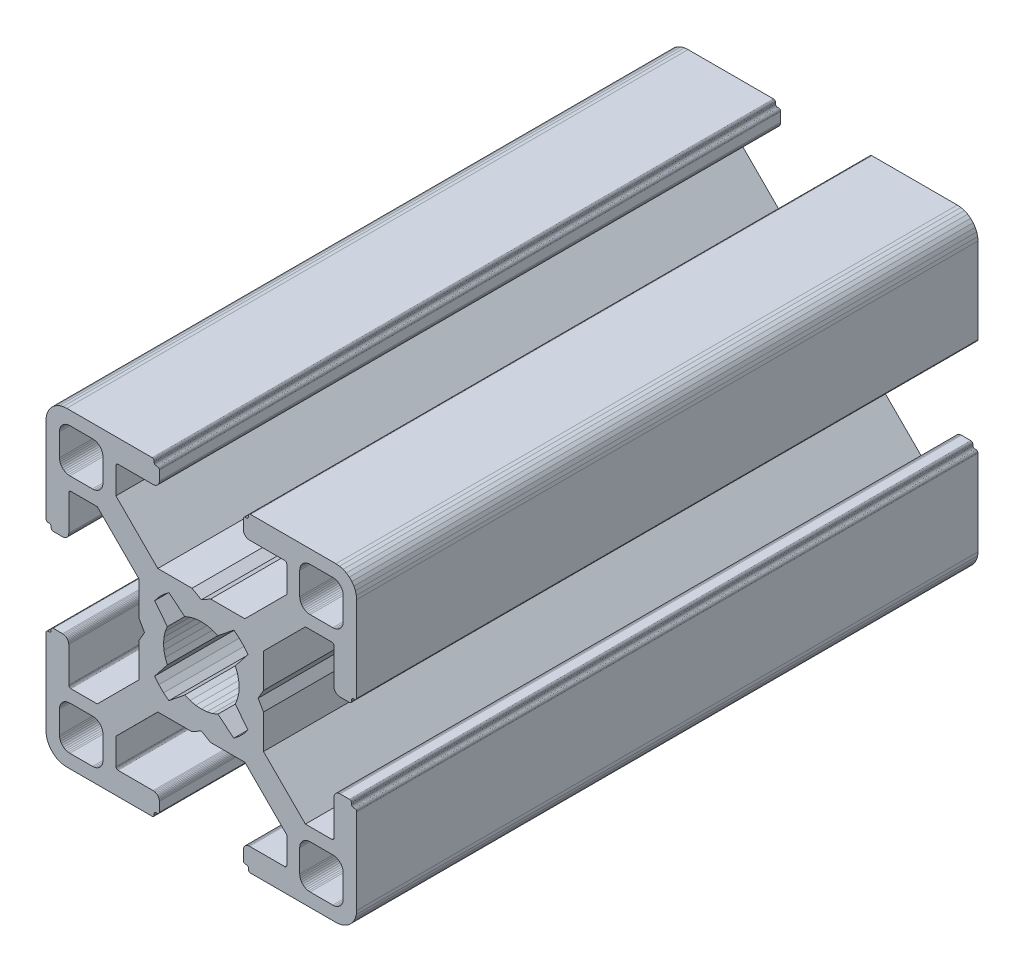
SolidWorks part; units mm, degrees
ref_plane "Front Plane" through (0, 0, 0) normal (0, 0, 1) x (1, 0, 0)
ref_plane "Top Plane" through (0, 0, 0) normal (0, 1, 0) x (1, 0, 0)
ref_plane "Right Plane" through (0, 0, 0) normal (1, 0, 0) x (0, 0, -1)
ref_plane "Plane1" through (0, 0, 0) normal (0, 0, 1) x (1, 0, 0)
sketch "Sketch1" plane through (0, 0, 0) normal (0, 0, 1) x (1, 0, 0)
  line L0 (28.3473, 29.9696) -> (28, 30)
  line L1 (28, 30) -> (19.75, 30)
  line L2 (19.75, 30) -> (19.7153, 29.997)
  line L3 (19.7153, 29.997) -> (19.6816, 29.9879)
  line L4 (19.6816, 29.9879) -> (19.65, 29.9732)
  line L5 (19.65, 29.9732) -> (19.6214, 29.9532)
  line L6 (19.6214, 29.9532) -> (19.5968, 29.9286)
  line L7 (19.5968, 29.9286) -> (19.5768, 29.9)
  line L8 (19.5768, 29.9) -> (19.5621, 29.8684)
  line L9 (19.5621, 29.8684) -> (19.553, 29.8347)
  line L10 (19.553, 29.8347) -> (19.55, 29.8)
  line L11 (19.55, 29.8) -> (19.55, 29.7)
  line L12 (19.55, 29.7) -> (19.547, 29.6653)
  line L13 (19.547, 29.6653) -> (19.5379, 29.6316)
  line L14 (19.5379, 29.6316) -> (19.5232, 29.6)
  line L15 (19.5232, 29.6) -> (19.5032, 29.5714)
  line L16 (19.5032, 29.5714) -> (19.4786, 29.5468)
  line L17 (19.4786, 29.5468) -> (19.45, 29.5268)
  line L18 (19.45, 29.5268) -> (19.4184, 29.5121)
  line L19 (19.4184, 29.5121) -> (19.3847, 29.503)
  line L20 (19.3847, 29.503) -> (19.35, 29.5)
  line L21 (19.35, 29.5) -> (19.25, 29.5)
  line L22 (19.25, 29.5) -> (19.2153, 29.497)
  line L23 (19.2153, 29.497) -> (19.1816, 29.4879)
  line L24 (19.1816, 29.4879) -> (19.15, 29.4732)
  line L25 (19.15, 29.4732) -> (19.1214, 29.4532)
  line L26 (19.1214, 29.4532) -> (19.0968, 29.4286)
  line L27 (19.0968, 29.4286) -> (19.0768, 29.4)
  line L28 (19.0768, 29.4) -> (19.0621, 29.3684)
  line L29 (19.0621, 29.3684) -> (19.053, 29.3347)
  line L30 (19.053, 29.3347) -> (19.05, 29.3)
  line L31 (19.05, 29.3) -> (19.05, 28.4)
  line L32 (19.05, 28.4) -> (19.0591, 28.2958)
  line L33 (19.0591, 28.2958) -> (19.0862, 28.1948)
  line L34 (19.0862, 28.1948) -> (19.1304, 28.1)
  line L35 (19.1304, 28.1) -> (19.1904, 28.0143)
  line L36 (19.1904, 28.0143) -> (19.2643, 27.9404)
  line L37 (19.2643, 27.9404) -> (19.35, 27.8804)
  line L38 (19.35, 27.8804) -> (19.4448, 27.8362)
  line L39 (19.4448, 27.8362) -> (19.5458, 27.8091)
  line L40 (19.5458, 27.8091) -> (19.65, 27.8)
  line L41 (19.65, 27.8) -> (23.05, 27.8)
  line L42 (23.05, 27.8) -> (23.0847, 27.7969)
  line L43 (23.0847, 27.7969) -> (23.1184, 27.7879)
  line L44 (23.1184, 27.7879) -> (23.15, 27.7732)
  line L45 (23.15, 27.7732) -> (23.1786, 27.7532)
  line L46 (23.1786, 27.7532) -> (23.2032, 27.7285)
  line L47 (23.2032, 27.7285) -> (23.2232, 27.7)
  line L48 (23.2232, 27.7) -> (23.2379, 27.6684)
  line L49 (23.2379, 27.6684) -> (23.247, 27.6347)
  line L50 (23.247, 27.6347) -> (23.25, 27.6)
  line L51 (23.25, 27.6) -> (23.25, 25.05)
  line L52 (23.25, 25.05) -> (19.2045, 21)
  line L53 (19.2045, 21) -> (15.9, 21)
  line L54 (15.9, 21) -> (15, 20.4848)
  line L55 (15, 20.4848) -> (14.1, 21)
  line L56 (14.1, 21) -> (10.7955, 21)
  line L57 (10.7955, 21) -> (7.9973, 23.8013)
  line L58 (7.9973, 23.8013) -> (6.75, 25.05)
  line L59 (6.75, 25.05) -> (6.75, 27.6)
  line L60 (6.75, 27.6) -> (6.753, 27.6347)
  line L61 (6.753, 27.6347) -> (6.7621, 27.6684)
  line L62 (6.7621, 27.6684) -> (6.7768, 27.7)
  line L63 (6.7768, 27.7) -> (6.7968, 27.7285)
  line L64 (6.7968, 27.7285) -> (6.8215, 27.7532)
  line L65 (6.8215, 27.7532) -> (6.85, 27.7732)
  line L66 (6.85, 27.7732) -> (6.8816, 27.7879)
  line L67 (6.8816, 27.7879) -> (6.9153, 27.7969)
  line L68 (6.9153, 27.7969) -> (6.95, 27.8)
  line L69 (6.95, 27.8) -> (10.35, 27.8)
  line L70 (10.35, 27.8) -> (10.4542, 27.8091)
  line L71 (10.4542, 27.8091) -> (10.5552, 27.8362)
  line L72 (10.5552, 27.8362) -> (10.65, 27.8804)
  line L73 (10.65, 27.8804) -> (10.7357, 27.9404)
  line L74 (10.7357, 27.9404) -> (10.8096, 28.0143)
  line L75 (10.8096, 28.0143) -> (10.8696, 28.1)
  line L76 (10.8696, 28.1) -> (10.9138, 28.1948)
  line L77 (10.9138, 28.1948) -> (10.9409, 28.2958)
  line L78 (10.9409, 28.2958) -> (10.95, 28.4)
  line L79 (10.95, 28.4) -> (10.95, 29.3)
  line L80 (10.95, 29.3) -> (10.947, 29.3347)
  line L81 (10.947, 29.3347) -> (10.938, 29.3684)
  line L82 (10.938, 29.3684) -> (10.9232, 29.4)
  line L83 (10.9232, 29.4) -> (10.9032, 29.4286)
  line L84 (10.9032, 29.4286) -> (10.8786, 29.4532)
  line L85 (10.8786, 29.4532) -> (10.85, 29.4732)
  line L86 (10.85, 29.4732) -> (10.8184, 29.4879)
  line L87 (10.8184, 29.4879) -> (10.7847, 29.497)
  line L88 (10.7847, 29.497) -> (10.75, 29.5)
  line L89 (10.75, 29.5) -> (10.65, 29.5)
  line L90 (10.65, 29.5) -> (10.6153, 29.503)
  line L91 (10.6153, 29.503) -> (10.5816, 29.5121)
  line L92 (10.5816, 29.5121) -> (10.55, 29.5268)
  line L93 (10.55, 29.5268) -> (10.5214, 29.5468)
  line L94 (10.5214, 29.5468) -> (10.4968, 29.5714)
  line L95 (10.4968, 29.5714) -> (10.4768, 29.6)
  line L96 (10.4768, 29.6) -> (10.4621, 29.6316)
  line L97 (10.4621, 29.6316) -> (10.453, 29.6653)
  line L98 (10.453, 29.6653) -> (10.45, 29.7)
  line L99 (10.45, 29.7) -> (10.45, 29.8)
  line L100 (10.45, 29.8) -> (10.447, 29.8347)
  line L101 (10.447, 29.8347) -> (10.4379, 29.8684)
  line L102 (10.4379, 29.8684) -> (10.4232, 29.9)
  line L103 (10.4232, 29.9) -> (10.4032, 29.9286)
  line L104 (10.4032, 29.9286) -> (10.3786, 29.9532)
  line L105 (10.3786, 29.9532) -> (10.35, 29.9732)
  line L106 (10.35, 29.9732) -> (10.3184, 29.9879)
  line L107 (10.3184, 29.9879) -> (10.2847, 29.997)
  line L108 (10.2847, 29.997) -> (10.25, 30)
  line L109 (10.25, 30) -> (2, 30)
  line L110 (2, 30) -> (1.6527, 29.9696)
  line L111 (1.6527, 29.9696) -> (1.316, 29.8794)
  line L112 (1.316, 29.8794) -> (1, 29.7321)
  line L113 (1, 29.7321) -> (0.7144, 29.5321)
  line L114 (0.7144, 29.5321) -> (0.4679, 29.2856)
  line L115 (0.4679, 29.2856) -> (0.2679, 29)
  line L116 (0.2679, 29) -> (0.1206, 28.684)
  line L117 (0.1206, 28.684) -> (0.0304, 28.3473)
  line L118 (0.0304, 28.3473) -> (0, 28)
  line L119 (0, 28) -> (0, 19.75)
  line L120 (0, 19.75) -> (0.003, 19.7153)
  line L121 (0.003, 19.7153) -> (0.0121, 19.6816)
  line L122 (0.0121, 19.6816) -> (0.0268, 19.65)
  line L123 (0.0268, 19.65) -> (0.0468, 19.6214)
  line L124 (0.0468, 19.6214) -> (0.0714, 19.5968)
  line L125 (0.0714, 19.5968) -> (0.1, 19.5768)
  line L126 (0.1, 19.5768) -> (0.1316, 19.5621)
  line L127 (0.1316, 19.5621) -> (0.1653, 19.553)
  line L128 (0.1653, 19.553) -> (0.2, 19.55)
  line L129 (0.2, 19.55) -> (0.3, 19.55)
  line L130 (0.3, 19.55) -> (0.3347, 19.547)
  line L131 (0.3347, 19.547) -> (0.3684, 19.5379)
  line L132 (0.3684, 19.5379) -> (0.4, 19.5232)
  line L133 (0.4, 19.5232) -> (0.4286, 19.5032)
  line L134 (0.4286, 19.5032) -> (0.4532, 19.4786)
  line L135 (0.4532, 19.4786) -> (0.4732, 19.45)
  line L136 (0.4732, 19.45) -> (0.4879, 19.4184)
  line L137 (0.4879, 19.4184) -> (0.497, 19.3847)
  line L138 (0.497, 19.3847) -> (0.5, 19.35)
  line L139 (0.5, 19.35) -> (0.5, 19.25)
  line L140 (0.5, 19.25) -> (0.503, 19.2153)
  line L141 (0.503, 19.2153) -> (0.5121, 19.1816)
  line L142 (0.5121, 19.1816) -> (0.5268, 19.15)
  line L143 (0.5268, 19.15) -> (0.5468, 19.1214)
  line L144 (0.5468, 19.1214) -> (0.5714, 19.0968)
  line L145 (0.5714, 19.0968) -> (0.6, 19.0768)
  line L146 (0.6, 19.0768) -> (0.6316, 19.0621)
  line L147 (0.6316, 19.0621) -> (0.6653, 19.053)
  line L148 (0.6653, 19.053) -> (0.7, 19.05)
  line L149 (0.7, 19.05) -> (1.6, 19.05)
  line L150 (1.6, 19.05) -> (1.7042, 19.0591)
  line L151 (1.7042, 19.0591) -> (1.8052, 19.0862)
  line L152 (1.8052, 19.0862) -> (1.9, 19.1304)
  line L153 (1.9, 19.1304) -> (1.9857, 19.1904)
  line L154 (1.9857, 19.1904) -> (2.0596, 19.2643)
  line L155 (2.0596, 19.2643) -> (2.1196, 19.35)
  line L156 (2.1196, 19.35) -> (2.1638, 19.4448)
  line L157 (2.1638, 19.4448) -> (2.1909, 19.5458)
  line L158 (2.1909, 19.5458) -> (2.2, 19.65)
  line L159 (2.2, 19.65) -> (2.2, 23.05)
  line L160 (2.2, 23.05) -> (2.203, 23.0847)
  line L161 (2.203, 23.0847) -> (2.2121, 23.1184)
  line L162 (2.2121, 23.1184) -> (2.2268, 23.15)
  line L163 (2.2268, 23.15) -> (2.2468, 23.1786)
  line L164 (2.2468, 23.1786) -> (2.2714, 23.2032)
  line L165 (2.2714, 23.2032) -> (2.3, 23.2232)
  line L166 (2.3, 23.2232) -> (2.3316, 23.2379)
  line L167 (2.3316, 23.2379) -> (2.3653, 23.247)
  line L168 (2.3653, 23.247) -> (2.4, 23.25)
  line L169 (2.4, 23.25) -> (4.95, 23.25)
  line L170 (4.95, 23.25) -> (7.9973, 20.2027)
  line L171 (7.9973, 20.2027) -> (8.9955, 19.2045)
  line L172 (8.9955, 19.2045) -> (8.9955, 15.9)
  line L173 (8.9955, 15.9) -> (9.5151, 15)
  line L174 (9.5151, 15) -> (8.9955, 14.1)
  line L175 (8.9955, 14.1) -> (8.9955, 10.7955)
  line L176 (8.9955, 10.7955) -> (4.95, 6.75)
  line L177 (4.95, 6.75) -> (2.4, 6.75)
  line L178 (2.4, 6.75) -> (2.3653, 6.753)
  line L179 (2.3653, 6.753) -> (2.3316, 6.7621)
  line L180 (2.3316, 6.7621) -> (2.3, 6.7768)
  line L181 (2.3, 6.7768) -> (2.2714, 6.7968)
  line L182 (2.2714, 6.7968) -> (2.2468, 6.8214)
  line L183 (2.2468, 6.8214) -> (2.2268, 6.85)
  line L184 (2.2268, 6.85) -> (2.2121, 6.8816)
  line L185 (2.2121, 6.8816) -> (2.203, 6.9153)
  line L186 (2.203, 6.9153) -> (2.2, 6.95)
  line L187 (2.2, 6.95) -> (2.2, 10.35)
  line L188 (2.2, 10.35) -> (2.1909, 10.4542)
  line L189 (2.1909, 10.4542) -> (2.1638, 10.5552)
  line L190 (2.1638, 10.5552) -> (2.1196, 10.65)
  line L191 (2.1196, 10.65) -> (2.0596, 10.7357)
  line L192 (2.0596, 10.7357) -> (1.9857, 10.8096)
  line L193 (1.9857, 10.8096) -> (1.9, 10.8696)
  line L194 (1.9, 10.8696) -> (1.8052, 10.9138)
  line L195 (1.8052, 10.9138) -> (1.7042, 10.9409)
  line L196 (1.7042, 10.9409) -> (1.6, 10.95)
  line L197 (1.6, 10.95) -> (0.7, 10.95)
  line L198 (0.7, 10.95) -> (0.6653, 10.9469)
  line L199 (0.6653, 10.9469) -> (0.6316, 10.9379)
  line L200 (0.6316, 10.9379) -> (0.6, 10.9232)
  line L201 (0.6, 10.9232) -> (0.5715, 10.9032)
  line L202 (0.5715, 10.9032) -> (0.5468, 10.8785)
  line L203 (0.5468, 10.8785) -> (0.5268, 10.85)
  line L204 (0.5268, 10.85) -> (0.5121, 10.8184)
  line L205 (0.5121, 10.8184) -> (0.503, 10.7847)
  line L206 (0.503, 10.7847) -> (0.5, 10.75)
  line L207 (0.5, 10.75) -> (0.5, 10.65)
  line L208 (0.5, 10.65) -> (0.497, 10.6153)
  line L209 (0.497, 10.6153) -> (0.4879, 10.5816)
  line L210 (0.4879, 10.5816) -> (0.4732, 10.55)
  line L211 (0.4732, 10.55) -> (0.4532, 10.5214)
  line L212 (0.4532, 10.5214) -> (0.4286, 10.4968)
  line L213 (0.4286, 10.4968) -> (0.4, 10.4768)
  line L214 (0.4, 10.4768) -> (0.3684, 10.4621)
  line L215 (0.3684, 10.4621) -> (0.3347, 10.453)
  line L216 (0.3347, 10.453) -> (0.3, 10.45)
  line L217 (0.3, 10.45) -> (0.2, 10.45)
  line L218 (0.2, 10.45) -> (0.1653, 10.447)
  line L219 (0.1653, 10.447) -> (0.1316, 10.4379)
  line L220 (0.1316, 10.4379) -> (0.1, 10.4232)
  line L221 (0.1, 10.4232) -> (0.0714, 10.4032)
  line L222 (0.0714, 10.4032) -> (0.0468, 10.3786)
  line L223 (0.0468, 10.3786) -> (0.0268, 10.35)
  line L224 (0.0268, 10.35) -> (0.0121, 10.3184)
  line L225 (0.0121, 10.3184) -> (0.003, 10.2847)
  line L226 (0.003, 10.2847) -> (0, 10.25)
  line L227 (0, 10.25) -> (0, 2)
  line L228 (0, 2) -> (0.0304, 1.6527)
  line L229 (0.0304, 1.6527) -> (0.1206, 1.316)
  line L230 (0.1206, 1.316) -> (0.2679, 1)
  line L231 (0.2679, 1) -> (0.4679, 0.7144)
  line L232 (0.4679, 0.7144) -> (0.7144, 0.4679)
  line L233 (0.7144, 0.4679) -> (1, 0.2679)
  line L234 (1, 0.2679) -> (1.316, 0.1206)
  line L235 (1.316, 0.1206) -> (1.6527, 0.0304)
  line L236 (1.6527, 0.0304) -> (2, 0)
  line L237 (2, 0) -> (10.25, 0)
  line L238 (10.25, 0) -> (10.2847, 0.003)
  line L239 (10.2847, 0.003) -> (10.3184, 0.0121)
  line L240 (10.3184, 0.0121) -> (10.35, 0.0268)
  line L241 (10.35, 0.0268) -> (10.3786, 0.0468)
  line L242 (10.3786, 0.0468) -> (10.4032, 0.0714)
  line L243 (10.4032, 0.0714) -> (10.4232, 0.1)
  line L244 (10.4232, 0.1) -> (10.4379, 0.1316)
  line L245 (10.4379, 0.1316) -> (10.447, 0.1653)
  line L246 (10.447, 0.1653) -> (10.45, 0.2)
  line L247 (10.45, 0.2) -> (10.45, 0.3)
  line L248 (10.45, 0.3) -> (10.453, 0.3347)
  line L249 (10.453, 0.3347) -> (10.4621, 0.3684)
  line L250 (10.4621, 0.3684) -> (10.4768, 0.4)
  line L251 (10.4768, 0.4) -> (10.4968, 0.4286)
  line L252 (10.4968, 0.4286) -> (10.5214, 0.4532)
  line L253 (10.5214, 0.4532) -> (10.55, 0.4732)
  line L254 (10.55, 0.4732) -> (10.5816, 0.4879)
  line L255 (10.5816, 0.4879) -> (10.6153, 0.497)
  line L256 (10.6153, 0.497) -> (10.65, 0.5)
  line L257 (10.65, 0.5) -> (10.75, 0.5)
  line L258 (10.75, 0.5) -> (10.7847, 0.503)
  line L259 (10.7847, 0.503) -> (10.8184, 0.5121)
  line L260 (10.8184, 0.5121) -> (10.85, 0.5268)
  line L261 (10.85, 0.5268) -> (10.8785, 0.5468)
  line L262 (10.8785, 0.5468) -> (10.9032, 0.5715)
  line L263 (10.9032, 0.5715) -> (10.9232, 0.6)
  line L264 (10.9232, 0.6) -> (10.9379, 0.6316)
  line L265 (10.9379, 0.6316) -> (10.9469, 0.6653)
  line L266 (10.9469, 0.6653) -> (10.95, 0.7)
  line L267 (10.95, 0.7) -> (10.95, 1.6)
  line L268 (10.95, 1.6) -> (10.9409, 1.7042)
  line L269 (10.9409, 1.7042) -> (10.9138, 1.8052)
  line L270 (10.9138, 1.8052) -> (10.8696, 1.9)
  line L271 (10.8696, 1.9) -> (10.8096, 1.9857)
  line L272 (10.8096, 1.9857) -> (10.7357, 2.0596)
  line L273 (10.7357, 2.0596) -> (10.65, 2.1196)
  line L274 (10.65, 2.1196) -> (10.5552, 2.1638)
  line L275 (10.5552, 2.1638) -> (10.4542, 2.1909)
  line L276 (10.4542, 2.1909) -> (10.35, 2.2)
  line L277 (10.35, 2.2) -> (6.95, 2.2)
  line L278 (6.95, 2.2) -> (6.9153, 2.203)
  line L279 (6.9153, 2.203) -> (6.8816, 2.212)
  line L280 (6.8816, 2.212) -> (6.85, 2.2268)
  line L281 (6.85, 2.2268) -> (6.8215, 2.2468)
  line L282 (6.8215, 2.2468) -> (6.7968, 2.2714)
  line L283 (6.7968, 2.2714) -> (6.7768, 2.3)
  line L284 (6.7768, 2.3) -> (6.7621, 2.3316)
  line L285 (6.7621, 2.3316) -> (6.753, 2.3653)
  line L286 (6.753, 2.3653) -> (6.75, 2.4)
  line L287 (6.75, 2.4) -> (6.75, 4.95)
  line L288 (6.75, 4.95) -> (9.7875, 7.9908)
  line L289 (9.7875, 7.9908) -> (10.7955, 9)
  line L290 (10.7955, 9) -> (14.1, 9)
  line L291 (14.1, 9) -> (15, 9.5151)
  line L292 (15, 9.5151) -> (15.9, 9)
  line L293 (15.9, 9) -> (19.2045, 9)
  line L294 (19.2045, 9) -> (20.2126, 7.9908)
  line L295 (20.2126, 7.9908) -> (23.25, 4.95)
  line L296 (23.25, 4.95) -> (23.25, 2.4)
  line L297 (23.25, 2.4) -> (23.247, 2.3653)
  line L298 (23.247, 2.3653) -> (23.2379, 2.3316)
  line L299 (23.2379, 2.3316) -> (23.2232, 2.3)
  line L300 (23.2232, 2.3) -> (23.2032, 2.2714)
  line L301 (23.2032, 2.2714) -> (23.1786, 2.2468)
  line L302 (23.1786, 2.2468) -> (23.15, 2.2268)
  line L303 (23.15, 2.2268) -> (23.1184, 2.212)
  line L304 (23.1184, 2.212) -> (23.0847, 2.203)
  line L305 (23.0847, 2.203) -> (23.05, 2.2)
  line L306 (23.05, 2.2) -> (19.65, 2.2)
  line L307 (19.65, 2.2) -> (19.5458, 2.1909)
  line L308 (19.5458, 2.1909) -> (19.4448, 2.1638)
  line L309 (19.4448, 2.1638) -> (19.35, 2.1196)
  line L310 (19.35, 2.1196) -> (19.2643, 2.0596)
  line L311 (19.2643, 2.0596) -> (19.1904, 1.9857)
  line L312 (19.1904, 1.9857) -> (19.1304, 1.9)
  line L313 (19.1304, 1.9) -> (19.0862, 1.8052)
  line L314 (19.0862, 1.8052) -> (19.0591, 1.7042)
  line L315 (19.0591, 1.7042) -> (19.05, 1.6)
  line L316 (19.05, 1.6) -> (19.05, 0.7)
  line L317 (19.05, 0.7) -> (19.053, 0.6653)
  line L318 (19.053, 0.6653) -> (19.0621, 0.6316)
  line L319 (19.0621, 0.6316) -> (19.0768, 0.6)
  line L320 (19.0768, 0.6) -> (19.0968, 0.5714)
  line L321 (19.0968, 0.5714) -> (19.1214, 0.5468)
  line L322 (19.1214, 0.5468) -> (19.15, 0.5268)
  line L323 (19.15, 0.5268) -> (19.1816, 0.5121)
  line L324 (19.1816, 0.5121) -> (19.2153, 0.503)
  line L325 (19.2153, 0.503) -> (19.25, 0.5)
  line L326 (19.25, 0.5) -> (19.35, 0.5)
  line L327 (19.35, 0.5) -> (19.3847, 0.497)
  line L328 (19.3847, 0.497) -> (19.4184, 0.4879)
  line L329 (19.4184, 0.4879) -> (19.45, 0.4732)
  line L330 (19.45, 0.4732) -> (19.4786, 0.4532)
  line L331 (19.4786, 0.4532) -> (19.5032, 0.4286)
  line L332 (19.5032, 0.4286) -> (19.5232, 0.4)
  line L333 (19.5232, 0.4) -> (19.5379, 0.3684)
  line L334 (19.5379, 0.3684) -> (19.547, 0.3347)
  line L335 (19.547, 0.3347) -> (19.55, 0.3)
  line L336 (19.55, 0.3) -> (19.55, 0.2)
  line L337 (19.55, 0.2) -> (19.553, 0.1653)
  line L338 (19.553, 0.1653) -> (19.5621, 0.1316)
  line L339 (19.5621, 0.1316) -> (19.5768, 0.1)
  line L340 (19.5768, 0.1) -> (19.5968, 0.0714)
  line L341 (19.5968, 0.0714) -> (19.6214, 0.0468)
  line L342 (19.6214, 0.0468) -> (19.65, 0.0268)
  line L343 (19.65, 0.0268) -> (19.6816, 0.0121)
  line L344 (19.6816, 0.0121) -> (19.7153, 0.003)
  line L345 (19.7153, 0.003) -> (19.75, 0)
  line L346 (19.75, 0) -> (28, 0)
  line L347 (28, 0) -> (28.3473, 0.0304)
  line L348 (28.3473, 0.0304) -> (28.684, 0.1206)
  line L349 (28.684, 0.1206) -> (29, 0.2679)
  line L350 (29, 0.2679) -> (29.2856, 0.4679)
  line L351 (29.2856, 0.4679) -> (29.5321, 0.7144)
  line L352 (29.5321, 0.7144) -> (29.7321, 1)
  line L353 (29.7321, 1) -> (29.8794, 1.316)
  line L354 (29.8794, 1.316) -> (29.9696, 1.6527)
  line L355 (29.9696, 1.6527) -> (30, 2)
  line L356 (30, 2) -> (30, 10.25)
  line L357 (30, 10.25) -> (29.997, 10.2847)
  line L358 (29.997, 10.2847) -> (29.988, 10.3184)
  line L359 (29.988, 10.3184) -> (29.9732, 10.35)
  line L360 (29.9732, 10.35) -> (29.9532, 10.3785)
  line L361 (29.9532, 10.3785) -> (29.9286, 10.4032)
  line L362 (29.9286, 10.4032) -> (29.9, 10.4232)
  line L363 (29.9, 10.4232) -> (29.8684, 10.4379)
  line L364 (29.8684, 10.4379) -> (29.8347, 10.447)
  line L365 (29.8347, 10.447) -> (29.8, 10.45)
  line L366 (29.8, 10.45) -> (29.7, 10.45)
  line L367 (29.7, 10.45) -> (29.6649, 10.4534)
  line L368 (29.6649, 10.4534) -> (29.6312, 10.4624)
  line L369 (29.6312, 10.4624) -> (29.5996, 10.4772)
  line L370 (29.5996, 10.4772) -> (29.5711, 10.4972)
  line L371 (29.5711, 10.4972) -> (29.5464, 10.5218)
  line L372 (29.5464, 10.5218) -> (29.5264, 10.5504)
  line L373 (29.5264, 10.5504) -> (29.5117, 10.582)
  line L374 (29.5117, 10.582) -> (29.5027, 10.6156)
  line L375 (29.5027, 10.6156) -> (29.4996, 10.6504)
  line L376 (29.4996, 10.6504) -> (29.4996, 10.7504)
  line L377 (29.4996, 10.7504) -> (29.497, 10.7847)
  line L378 (29.497, 10.7847) -> (29.4879, 10.8184)
  line L379 (29.4879, 10.8184) -> (29.4732, 10.85)
  line L380 (29.4732, 10.85) -> (29.4532, 10.8785)
  line L381 (29.4532, 10.8785) -> (29.4286, 10.9032)
  line L382 (29.4286, 10.9032) -> (29.4, 10.9232)
  line L383 (29.4, 10.9232) -> (29.3684, 10.9379)
  line L384 (29.3684, 10.9379) -> (29.3347, 10.9469)
  line L385 (29.3347, 10.9469) -> (29.3, 10.95)
  line L386 (29.3, 10.95) -> (28.4, 10.95)
  line L387 (28.4, 10.95) -> (28.2958, 10.9409)
  line L388 (28.2958, 10.9409) -> (28.1948, 10.9138)
  line L389 (28.1948, 10.9138) -> (28.1, 10.8696)
  line L390 (28.1, 10.8696) -> (28.0143, 10.8096)
  line L391 (28.0143, 10.8096) -> (27.9404, 10.7357)
  line L392 (27.9404, 10.7357) -> (27.8804, 10.65)
  line L393 (27.8804, 10.65) -> (27.8362, 10.5552)
  line L394 (27.8362, 10.5552) -> (27.8091, 10.4542)
  line L395 (27.8091, 10.4542) -> (27.8, 10.35)
  line L396 (27.8, 10.35) -> (27.8, 6.95)
  line L397 (27.8, 6.95) -> (27.797, 6.9153)
  line L398 (27.797, 6.9153) -> (27.7879, 6.8816)
  line L399 (27.7879, 6.8816) -> (27.7732, 6.85)
  line L400 (27.7732, 6.85) -> (27.7532, 6.8214)
  line L401 (27.7532, 6.8214) -> (27.7286, 6.7968)
  line L402 (27.7286, 6.7968) -> (27.7, 6.7768)
  line L403 (27.7, 6.7768) -> (27.6684, 6.7621)
  line L404 (27.6684, 6.7621) -> (27.6347, 6.753)
  line L405 (27.6347, 6.753) -> (27.6, 6.75)
  line L406 (27.6, 6.75) -> (25.05, 6.75)
  line L407 (25.05, 6.75) -> (23.8092, 7.9908)
  line L408 (23.8092, 7.9908) -> (21.0045, 10.7955)
  line L409 (21.0045, 10.7955) -> (21.0045, 14.1)
  line L410 (21.0045, 14.1) -> (20.4849, 15)
  line L411 (20.4849, 15) -> (21.0045, 15.9)
  line L412 (21.0045, 15.9) -> (21.0045, 19.2045)
  line L413 (21.0045, 19.2045) -> (25.05, 23.25)
  line L414 (25.05, 23.25) -> (27.6, 23.25)
  line L415 (27.6, 23.25) -> (27.6347, 23.247)
  line L416 (27.6347, 23.247) -> (27.6684, 23.2379)
  line L417 (27.6684, 23.2379) -> (27.7, 23.2232)
  line L418 (27.7, 23.2232) -> (27.7286, 23.2032)
  line L419 (27.7286, 23.2032) -> (27.7532, 23.1786)
  line L420 (27.7532, 23.1786) -> (27.7732, 23.15)
  line L421 (27.7732, 23.15) -> (27.7879, 23.1184)
  line L422 (27.7879, 23.1184) -> (27.797, 23.0847)
  line L423 (27.797, 23.0847) -> (27.8, 23.05)
  line L424 (27.8, 23.05) -> (27.8, 19.65)
  line L425 (27.8, 19.65) -> (27.8091, 19.5458)
  line L426 (27.8091, 19.5458) -> (27.8362, 19.4448)
  line L427 (27.8362, 19.4448) -> (27.8804, 19.35)
  line L428 (27.8804, 19.35) -> (27.9404, 19.2643)
  line L429 (27.9404, 19.2643) -> (28.0143, 19.1904)
  line L430 (28.0143, 19.1904) -> (28.1, 19.1304)
  line L431 (28.1, 19.1304) -> (28.1948, 19.0862)
  line L432 (28.1948, 19.0862) -> (28.2958, 19.0591)
  line L433 (28.2958, 19.0591) -> (28.4, 19.05)
  line L434 (28.4, 19.05) -> (29.3, 19.05)
  line L435 (29.3, 19.05) -> (29.3347, 19.053)
  line L436 (29.3347, 19.053) -> (29.3684, 19.0621)
  line L437 (29.3684, 19.0621) -> (29.4, 19.0768)
  line L438 (29.4, 19.0768) -> (29.4282, 19.0971)
  line L439 (29.4282, 19.0971) -> (29.4528, 19.1218)
  line L440 (29.4528, 19.1218) -> (29.4728, 19.1504)
  line L441 (29.4728, 19.1504) -> (29.4876, 19.182)
  line L442 (29.4876, 19.182) -> (29.4966, 19.2156)
  line L443 (29.4966, 19.2156) -> (29.4996, 19.2504)
  line L444 (29.4996, 19.2504) -> (29.4996, 19.3504)
  line L445 (29.4996, 19.3504) -> (29.5027, 19.3851)
  line L446 (29.5027, 19.3851) -> (29.5117, 19.4188)
  line L447 (29.5117, 19.4188) -> (29.5264, 19.4504)
  line L448 (29.5264, 19.4504) -> (29.5464, 19.4789)
  line L449 (29.5464, 19.4789) -> (29.5711, 19.5036)
  line L450 (29.5711, 19.5036) -> (29.5996, 19.5236)
  line L451 (29.5996, 19.5236) -> (29.6312, 19.5383)
  line L452 (29.6312, 19.5383) -> (29.6649, 19.5473)
  line L453 (29.6649, 19.5473) -> (29.7, 19.55)
  line L454 (29.7, 19.55) -> (29.8, 19.55)
  line L455 (29.8, 19.55) -> (29.8347, 19.553)
  line L456 (29.8347, 19.553) -> (29.8684, 19.5621)
  line L457 (29.8684, 19.5621) -> (29.9, 19.5768)
  line L458 (29.9, 19.5768) -> (29.9286, 19.5968)
  line L459 (29.9286, 19.5968) -> (29.9532, 19.6214)
  line L460 (29.9532, 19.6214) -> (29.9732, 19.65)
  line L461 (29.9732, 19.65) -> (29.9879, 19.6816)
  line L462 (29.9879, 19.6816) -> (29.997, 19.7153)
  line L463 (29.997, 19.7153) -> (30, 19.75)
  line L464 (30, 19.75) -> (30, 28)
  line L465 (30, 28) -> (29.9696, 28.3473)
  line L466 (29.9696, 28.3473) -> (29.8794, 28.684)
  line L467 (29.8794, 28.684) -> (29.7321, 29)
  line L468 (29.7321, 29) -> (29.5321, 29.2856)
  line L469 (29.5321, 29.2856) -> (29.2856, 29.5321)
  line L470 (29.2856, 29.5321) -> (29, 29.7321)
  line L471 (29, 29.7321) -> (28.684, 29.8794)
  line L472 (28.684, 29.8794) -> (28.3473, 29.9696)
  line L473 (1.3, 25.5) -> (1.3, 27.7)
  line L474 (1.3, 27.7) -> (1.3123, 27.8564)
  line L475 (1.3123, 27.8564) -> (1.3489, 28.009)
  line L476 (1.3489, 28.009) -> (1.409, 28.154)
  line L477 (1.409, 28.154) -> (1.491, 28.2878)
  line L478 (1.491, 28.2878) -> (1.5929, 28.4071)
  line L479 (1.5929, 28.4071) -> (1.7122, 28.509)
  line L480 (1.7122, 28.509) -> (1.846, 28.591)
  line L481 (1.846, 28.591) -> (1.991, 28.6511)
  line L482 (1.991, 28.6511) -> (2.1436, 28.6877)
  line L483 (2.1436, 28.6877) -> (2.3, 28.7)
  line L484 (2.3, 28.7) -> (4.5, 28.7)
  line L485 (4.5, 28.7) -> (4.6564, 28.6877)
  line L486 (4.6564, 28.6877) -> (4.809, 28.6511)
  line L487 (4.809, 28.6511) -> (4.954, 28.591)
  line L488 (4.954, 28.591) -> (5.0878, 28.509)
  line L489 (5.0878, 28.509) -> (5.2071, 28.4071)
  line L490 (5.2071, 28.4071) -> (5.309, 28.2878)
  line L491 (5.309, 28.2878) -> (5.391, 28.154)
  line L492 (5.391, 28.154) -> (5.4511, 28.009)
  line L493 (5.4511, 28.009) -> (5.4877, 27.8564)
  line L494 (5.4877, 27.8564) -> (5.5, 27.7)
  line L495 (5.5, 27.7) -> (5.5, 25.5)
  line L496 (5.5, 25.5) -> (5.4877, 25.3436)
  line L497 (5.4877, 25.3436) -> (5.4511, 25.191)
  line L498 (5.4511, 25.191) -> (5.391, 25.046)
  line L499 (5.391, 25.046) -> (5.309, 24.9122)
  line L500 (5.309, 24.9122) -> (5.2071, 24.7929)
  line L501 (5.2071, 24.7929) -> (5.0878, 24.691)
  line L502 (5.0878, 24.691) -> (4.954, 24.609)
  line L503 (4.954, 24.609) -> (4.809, 24.5489)
  line L504 (4.809, 24.5489) -> (4.6564, 24.5123)
  line L505 (4.6564, 24.5123) -> (4.5, 24.5)
  line L506 (4.5, 24.5) -> (2.3, 24.5)
  line L507 (2.3, 24.5) -> (2.1436, 24.5123)
  line L508 (2.1436, 24.5123) -> (1.991, 24.5489)
  line L509 (1.991, 24.5489) -> (1.846, 24.609)
  line L510 (1.846, 24.609) -> (1.7122, 24.691)
  line L511 (1.7122, 24.691) -> (1.5929, 24.7929)
  line L512 (1.5929, 24.7929) -> (1.491, 24.9122)
  line L513 (1.491, 24.9122) -> (1.409, 25.046)
  line L514 (1.409, 25.046) -> (1.3489, 25.191)
  line L515 (1.3489, 25.191) -> (1.3123, 25.3436)
  line L516 (1.3123, 25.3436) -> (1.3, 25.5)
  line L517 (25.3436, 28.6877) -> (25.5, 28.7)
  line L518 (25.5, 28.7) -> (27.7, 28.7)
  line L519 (27.7, 28.7) -> (27.8564, 28.6877)
  line L520 (27.8564, 28.6877) -> (28.009, 28.6511)
  line L521 (28.009, 28.6511) -> (28.154, 28.591)
  line L522 (28.154, 28.591) -> (28.2878, 28.509)
  line L523 (28.2878, 28.509) -> (28.4071, 28.4071)
  line L524 (28.4071, 28.4071) -> (28.509, 28.2878)
  line L525 (28.509, 28.2878) -> (28.591, 28.154)
  line L526 (28.591, 28.154) -> (28.6511, 28.009)
  line L527 (28.6511, 28.009) -> (28.6877, 27.8564)
  line L528 (28.6877, 27.8564) -> (28.7, 27.7)
  line L529 (28.7, 27.7) -> (28.7, 25.5)
  line L530 (28.7, 25.5) -> (28.6877, 25.3436)
  line L531 (28.6877, 25.3436) -> (28.6511, 25.191)
  line L532 (28.6511, 25.191) -> (28.591, 25.046)
  line L533 (28.591, 25.046) -> (28.509, 24.9122)
  line L534 (28.509, 24.9122) -> (28.4071, 24.7929)
  line L535 (28.4071, 24.7929) -> (28.2878, 24.691)
  line L536 (28.2878, 24.691) -> (28.154, 24.609)
  line L537 (28.154, 24.609) -> (28.009, 24.5489)
  line L538 (28.009, 24.5489) -> (27.8564, 24.5123)
  line L539 (27.8564, 24.5123) -> (27.7, 24.5)
  line L540 (27.7, 24.5) -> (25.5, 24.5)
  line L541 (25.5, 24.5) -> (25.3436, 24.5123)
  line L542 (25.3436, 24.5123) -> (25.191, 24.5489)
  line L543 (25.191, 24.5489) -> (25.046, 24.609)
  line L544 (25.046, 24.609) -> (24.9122, 24.691)
  line L545 (24.9122, 24.691) -> (24.7929, 24.7929)
  line L546 (24.7929, 24.7929) -> (24.691, 24.9122)
  line L547 (24.691, 24.9122) -> (24.609, 25.046)
  line L548 (24.609, 25.046) -> (24.5489, 25.191)
  line L549 (24.5489, 25.191) -> (24.5123, 25.3436)
  line L550 (24.5123, 25.3436) -> (24.5, 25.5)
  line L551 (24.5, 25.5) -> (24.5, 27.7)
  line L552 (24.5, 27.7) -> (24.5123, 27.8564)
  line L553 (24.5123, 27.8564) -> (24.5489, 28.009)
  line L554 (24.5489, 28.009) -> (24.609, 28.154)
  line L555 (24.609, 28.154) -> (24.691, 28.2878)
  line L556 (24.691, 28.2878) -> (24.7929, 28.4071)
  line L557 (24.7929, 28.4071) -> (24.9122, 28.509)
  line L558 (24.9122, 28.509) -> (25.046, 28.591)
  line L559 (25.046, 28.591) -> (25.191, 28.6511)
  line L560 (25.191, 28.6511) -> (25.3436, 28.6877)
  line L561 (15, 18.65) -> (15.55, 18.6083)
  line L562 (15.55, 18.6083) -> (16.0875, 18.4842)
  line L563 (16.0875, 18.4842) -> (16.6001, 18.2806)
  line L564 (16.6001, 18.2806) -> (18.1359, 19.5184)
  line L565 (18.1359, 19.5184) -> (18.645, 19.1187)
  line L566 (18.645, 19.1187) -> (19.1036, 18.6621)
  line L567 (19.1036, 18.6621) -> (19.5053, 18.1547)
  line L568 (19.5053, 18.1547) -> (18.2806, 16.6001)
  line L569 (18.2806, 16.6001) -> (18.4842, 16.0875)
  line L570 (18.4842, 16.0875) -> (18.6083, 15.55)
  line L571 (18.6083, 15.55) -> (18.65, 15)
  line L572 (18.65, 15) -> (18.6083, 14.45)
  line L573 (18.6083, 14.45) -> (18.4842, 13.9125)
  line L574 (18.4842, 13.9125) -> (18.2806, 13.3999)
  line L575 (18.2806, 13.3999) -> (19.5053, 11.8453)
  line L576 (19.5053, 11.8453) -> (19.1036, 11.3379)
  line L577 (19.1036, 11.3379) -> (18.645, 10.8813)
  line L578 (18.645, 10.8813) -> (18.1359, 10.4816)
  line L579 (18.1359, 10.4816) -> (16.6001, 11.7194)
  line L580 (16.6001, 11.7194) -> (16.0875, 11.5158)
  line L581 (16.0875, 11.5158) -> (15.55, 11.3917)
  line L582 (15.55, 11.3917) -> (15, 11.35)
  line L583 (15, 11.35) -> (14.45, 11.3917)
  line L584 (14.45, 11.3917) -> (13.9125, 11.5158)
  line L585 (13.9125, 11.5158) -> (13.3999, 11.7194)
  line L586 (13.3999, 11.7194) -> (11.8641, 10.4816)
  line L587 (11.8641, 10.4816) -> (11.355, 10.8813)
  line L588 (11.355, 10.8813) -> (10.8964, 11.3379)
  line L589 (10.8964, 11.3379) -> (10.4947, 11.8453)
  line L590 (10.4947, 11.8453) -> (11.7194, 13.3999)
  line L591 (11.7194, 13.3999) -> (11.5158, 13.9125)
  line L592 (11.5158, 13.9125) -> (11.3917, 14.45)
  line L593 (11.3917, 14.45) -> (11.35, 15)
  line L594 (11.35, 15) -> (11.3917, 15.55)
  line L595 (11.3917, 15.55) -> (11.5158, 16.0875)
  line L596 (11.5158, 16.0875) -> (11.7194, 16.6001)
  line L597 (11.7194, 16.6001) -> (10.4947, 18.1547)
  line L598 (10.4947, 18.1547) -> (10.8964, 18.6621)
  line L599 (10.8964, 18.6621) -> (11.355, 19.1187)
  line L600 (11.355, 19.1187) -> (11.8641, 19.5184)
  line L601 (11.8641, 19.5184) -> (13.3999, 18.2806)
  line L602 (13.3999, 18.2806) -> (13.9125, 18.4842)
  line L603 (13.9125, 18.4842) -> (14.45, 18.6083)
  line L604 (14.45, 18.6083) -> (15, 18.65)
  line L605 (4.5, 1.3) -> (2.3, 1.3)
  line L606 (2.3, 1.3) -> (2.1436, 1.3123)
  line L607 (2.1436, 1.3123) -> (1.991, 1.3489)
  line L608 (1.991, 1.3489) -> (1.846, 1.409)
  line L609 (1.846, 1.409) -> (1.7122, 1.491)
  line L610 (1.7122, 1.491) -> (1.5929, 1.5929)
  line L611 (1.5929, 1.5929) -> (1.491, 1.7122)
  line L612 (1.491, 1.7122) -> (1.409, 1.846)
  line L613 (1.409, 1.846) -> (1.3489, 1.991)
  line L614 (1.3489, 1.991) -> (1.3123, 2.1436)
  line L615 (1.3123, 2.1436) -> (1.3, 2.3)
  line L616 (1.3, 2.3) -> (1.3, 4.5)
  line L617 (1.3, 4.5) -> (1.3123, 4.6564)
  line L618 (1.3123, 4.6564) -> (1.3489, 4.809)
  line L619 (1.3489, 4.809) -> (1.409, 4.954)
  line L620 (1.409, 4.954) -> (1.491, 5.0878)
  line L621 (1.491, 5.0878) -> (1.5929, 5.2071)
  line L622 (1.5929, 5.2071) -> (1.7122, 5.309)
  line L623 (1.7122, 5.309) -> (1.846, 5.391)
  line L624 (1.846, 5.391) -> (1.991, 5.4511)
  line L625 (1.991, 5.4511) -> (2.1436, 5.4877)
  line L626 (2.1436, 5.4877) -> (2.3, 5.5)
  line L627 (2.3, 5.5) -> (4.5, 5.5)
  line L628 (4.5, 5.5) -> (4.6564, 5.4877)
  line L629 (4.6564, 5.4877) -> (4.809, 5.4511)
  line L630 (4.809, 5.4511) -> (4.954, 5.391)
  line L631 (4.954, 5.391) -> (5.0878, 5.309)
  line L632 (5.0878, 5.309) -> (5.2071, 5.2071)
  line L633 (5.2071, 5.2071) -> (5.309, 5.0878)
  line L634 (5.309, 5.0878) -> (5.391, 4.954)
  line L635 (5.391, 4.954) -> (5.4511, 4.809)
  line L636 (5.4511, 4.809) -> (5.4877, 4.6564)
  line L637 (5.4877, 4.6564) -> (5.5, 4.5)
  line L638 (5.5, 4.5) -> (5.5, 2.3)
  line L639 (5.5, 2.3) -> (5.4877, 2.1436)
  line L640 (5.4877, 2.1436) -> (5.4511, 1.991)
  line L641 (5.4511, 1.991) -> (5.391, 1.846)
  line L642 (5.391, 1.846) -> (5.309, 1.7122)
  line L643 (5.309, 1.7122) -> (5.2071, 1.5929)
  line L644 (5.2071, 1.5929) -> (5.0878, 1.491)
  line L645 (5.0878, 1.491) -> (4.954, 1.409)
  line L646 (4.954, 1.409) -> (4.809, 1.3489)
  line L647 (4.809, 1.3489) -> (4.6564, 1.3123)
  line L648 (4.6564, 1.3123) -> (4.5, 1.3)
  line L649 (27.7, 1.3) -> (25.5, 1.3)
  line L650 (25.5, 1.3) -> (25.3436, 1.3123)
  line L651 (25.3436, 1.3123) -> (25.191, 1.3489)
  line L652 (25.191, 1.3489) -> (25.046, 1.409)
  line L653 (25.046, 1.409) -> (24.9122, 1.491)
  line L654 (24.9122, 1.491) -> (24.7929, 1.5929)
  line L655 (24.7929, 1.5929) -> (24.691, 1.7122)
  line L656 (24.691, 1.7122) -> (24.609, 1.846)
  line L657 (24.609, 1.846) -> (24.5489, 1.991)
  line L658 (24.5489, 1.991) -> (24.5123, 2.1436)
  line L659 (24.5123, 2.1436) -> (24.5, 2.3)
  line L660 (24.5, 2.3) -> (24.5, 4.5)
  line L661 (24.5, 4.5) -> (24.5123, 4.6564)
  line L662 (24.5123, 4.6564) -> (24.5489, 4.809)
  line L663 (24.5489, 4.809) -> (24.609, 4.954)
  line L664 (24.609, 4.954) -> (24.691, 5.0878)
  line L665 (24.691, 5.0878) -> (24.7929, 5.2071)
  line L666 (24.7929, 5.2071) -> (24.9122, 5.309)
  line L667 (24.9122, 5.309) -> (25.046, 5.391)
  line L668 (25.046, 5.391) -> (25.191, 5.4511)
  line L669 (25.191, 5.4511) -> (25.3436, 5.4877)
  line L670 (25.3436, 5.4877) -> (25.5, 5.5)
  line L671 (25.5, 5.5) -> (27.7, 5.5)
  line L672 (27.7, 5.5) -> (27.8564, 5.4877)
  line L673 (27.8564, 5.4877) -> (28.009, 5.4511)
  line L674 (28.009, 5.4511) -> (28.154, 5.391)
  line L675 (28.154, 5.391) -> (28.2878, 5.309)
  line L676 (28.2878, 5.309) -> (28.4071, 5.2071)
  line L677 (28.4071, 5.2071) -> (28.509, 5.0878)
  line L678 (28.509, 5.0878) -> (28.591, 4.954)
  line L679 (28.591, 4.954) -> (28.6511, 4.809)
  line L680 (28.6511, 4.809) -> (28.6877, 4.6564)
  line L681 (28.6877, 4.6564) -> (28.7, 4.5)
  line L682 (28.7, 4.5) -> (28.7, 2.3)
  line L683 (28.7, 2.3) -> (28.6877, 2.1436)
  line L684 (28.6877, 2.1436) -> (28.6511, 1.991)
  line L685 (28.6511, 1.991) -> (28.591, 1.846)
  line L686 (28.591, 1.846) -> (28.509, 1.7122)
  line L687 (28.509, 1.7122) -> (28.4071, 1.5929)
  line L688 (28.4071, 1.5929) -> (28.2878, 1.491)
  line L689 (28.2878, 1.491) -> (28.154, 1.409)
  line L690 (28.154, 1.409) -> (28.009, 1.3489)
  line L691 (28.009, 1.3489) -> (27.8564, 1.3123)
  line L692 (27.8564, 1.3123) -> (27.7, 1.3)
extrude "Boss-Extrude1" add sketch "Sketch1" against normal blind 60
